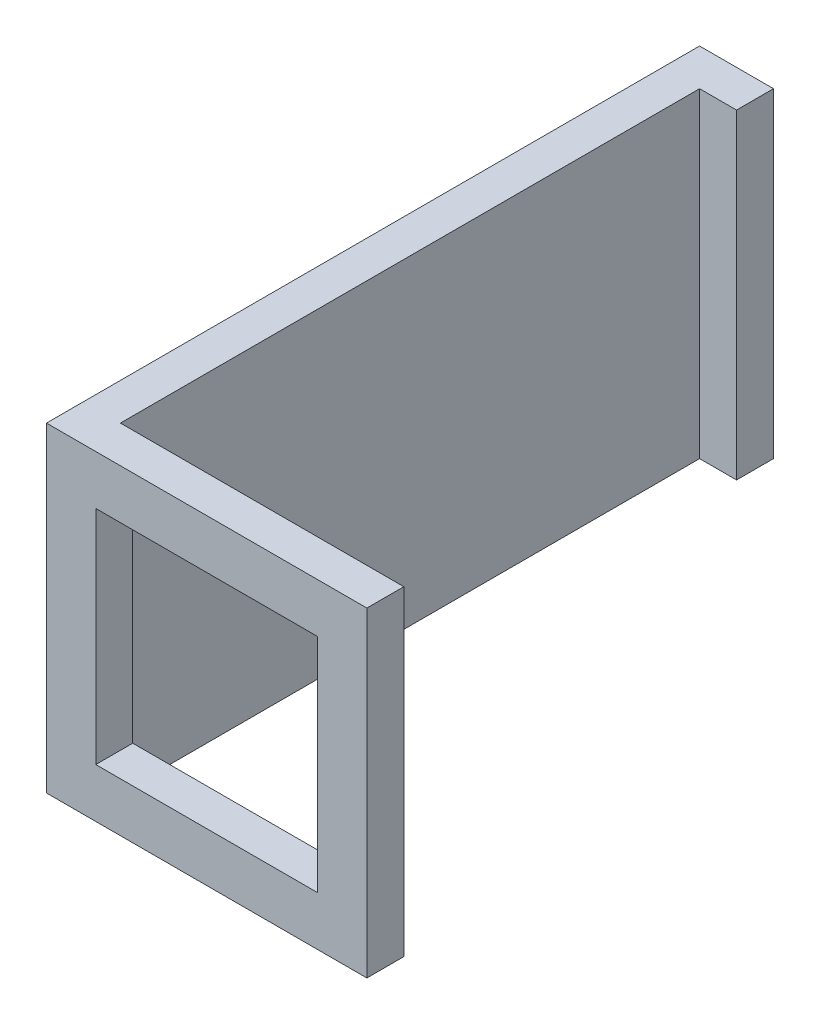
SolidWorks part; units mm, degrees
ref_plane "Front Plane" through (0, 0, 0) normal (0, 0, 1) x (1, 0, 0)
ref_plane "Top Plane" through (0, 0, 0) normal (0, 1, 0) x (1, 0, 0)
ref_plane "Right Plane" through (0, 0, 0) normal (1, 0, 0) x (0, 0, -1)
sketch "Sketch1" plane through (0, 0, 0) normal (0, 0, 1) x (1, 0, 0)
  line L0 (4.5, 4.5) -> (-4.5, 4.5)
  line L1 (6.5, -6.5) -> (-6.5, -6.5)
  line L2 (6.5, -6.5) -> (6.5, 6.5)
  line L3 (6.5, 6.5) -> (-6.5, 6.5)
  line L4 (-6.5, -6.5) -> (-6.5, 6.5)
  line L5 (6.5, -6.5) -> (-6.5, 6.5) construction
  line L6 (6.5, 6.5) -> (-6.5, -6.5) construction
  line L7 (-4.5, -4.5) -> (-4.5, 4.5)
  line L8 (4.5, -4.5) -> (-4.5, -4.5)
  line L9 (4.5, -4.5) -> (4.5, 4.5)
  point P0 (0, 0)
  dimension "D1" = 13
  dimension "D2" = 2
extrude "Boss-Extrude1" add sketch "Sketch1" along normal blind 1.5
sketch "Sketch2" plane through (0, 0, 0) normal (0, 0, -1) x (-1, 0, 0)
  line L1 (5, 6.5) -> (6.5, 6.5)
  line L2 (5, 6.5) -> (5, -6.5)
  line L3 (5, -6.5) -> (6.5, -6.5)
  line L4 (6.5, 6.5) -> (6.5, -6.5)
  line L5 (5, 6.5) -> (6.5, -6.5) construction
  line L6 (5, -6.5) -> (6.5, 6.5) construction
  point P0 (5.75, 0)
  dimension "D1" = 1.5
extrude "Boss-Extrude2" add sketch "Sketch2" along normal blind 25
sketch "Sketch3" plane through (-5, 0, 0) normal (1, 0, 0) x (0, 0, -1)
  line L1 (23.5, -6.5) -> (25, -6.5)
  line L2 (23.5, -6.5) -> (23.5, 6.5)
  line L3 (23.5, 6.5) -> (25, 6.5)
  line L4 (25, -6.5) -> (25, 6.5)
  line L5 (23.5, -6.5) -> (25, 6.5) construction
  line L6 (23.5, 6.5) -> (25, -6.5) construction
  point P0 (24.25, 0)
  dimension "D1" = 1.5
extrude "Boss-Extrude3" add sketch "Sketch3" along normal blind 1.5
